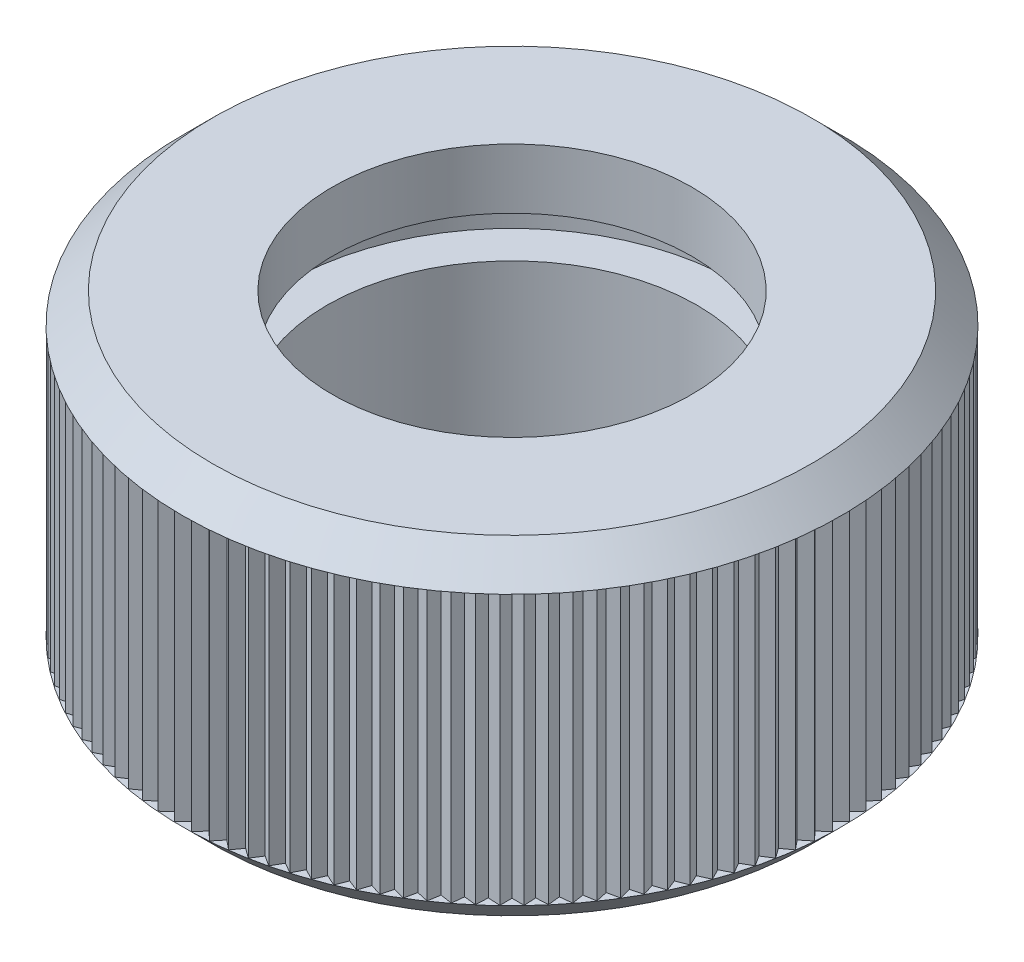
SolidWorks part; units mm, degrees
material "Латунь"
ref_plane "Спереди" through (0, 0, 0) normal (0, 0, 1) x (1, 0, 0)
ref_plane "Сверху" through (0, 0, 0) normal (0, 1, 0) x (1, 0, 0)
ref_plane "Справа" through (0, 0, 0) normal (1, 0, 0) x (0, 0, -1)
sketch "Эскиз1" plane through (0, 0, 0) normal (1, 0, 0) x (0, 0, -1)
  line L0 (6, 11) -> (6, 9)
  line L1 (0, 0) -> (11, 0) construction
  line L2 (0, 0) -> (0, 11) construction
  line L3 (0, 11) -> (11, 11) construction
  line L4 (11, 0) -> (11, 11)
  line L5 (6, 9) -> (7.5, 9)
  line L6 (7.5, 9) -> (7.5, 7.5)
  line L7 (7.5, 7.5) -> (6, 7.5)
  line L8 (6, 7.5) -> (6, 0)
  line L9 (6, 11) -> (11, 11)
  line L10 (6, 0) -> (11, 0)
  dimension "D1" = 11
  dimension "D2" = 11
  dimension "D3" = 6
  dimension "D4" = 1.5
  dimension "D5" = 2
revolve "Повернуть1" add sketch "Эскиз1" angle 360 about L2
chamfer "Фаска1" distance 1 angle 45 2 edges at (0, 0, -11) (0, 11, -11)
ref_plane "Плоскость2" through (0, 5.5, 0) normal (0, 1, 0) x (1, 0, 0)
sketch "Эскиз4" plane through (0, 5.5, 0) normal (0, 1, 0) x (1, 0, 0)
  line L0 (-11, 0) -> (11, 0) construction
  line L1 (-10.6959, 0) -> (-12.6959, 2)
  line L2 (-12.6959, 2) -> (-12.6959, -2)
  line L3 (-12.6959, 0) -> (-10.6959, 0)
  line L4 (-10.6959, 0) -> (-12.6959, -2)
  circle A0 centre (0, 0) radius 11 construction
  point P7 (-10.9959, 0.3)
  dimension "D1" = 45
  dimension "D2" = 0.3
  dimension "D3" = 2
extrude "Вырез-Вытянуть1" cut sketch "Эскиз4" against normal blind 4.5 and the other way blind 4.5
pattern_circular "Круговой массив1" count 120 over 360 about axis through (0, 0, 0) along (0, 1, 0) of "Вырез-Вытянуть1"
sketch "Эскиз5" plane through (0, 0, 0) normal (0, -1, 0) x (1, 0, 0)
  circle A0 centre (0, 0) radius 6.172
  dimension "D1" = 12.344
extrude "Вырез-Вытянуть2" cut sketch "Эскиз5" against normal up to surface (9 mm away)
cosmetic thread "Условное изображение резьбы1" parameters "D2"=14
chamfer "Фаска2" distance 0.828 angle 45 1 edges at (0, 0, -6.172)
